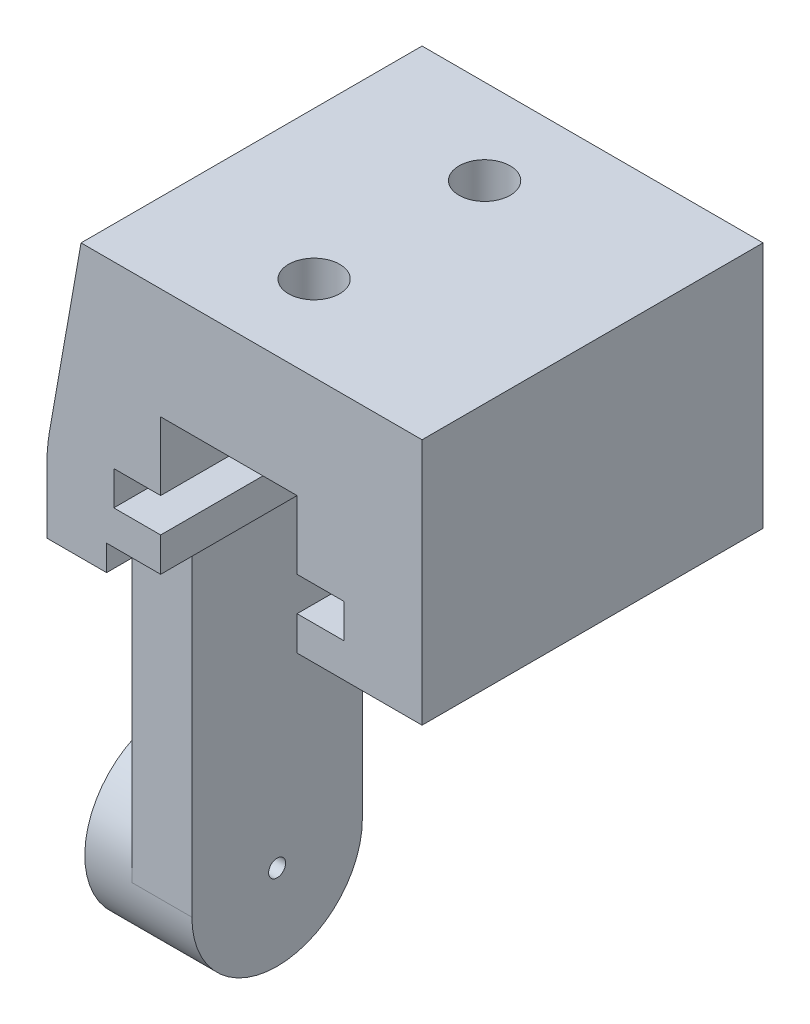
SolidWorks part; units mm, degrees
ref_plane "Front Plane" through (0, 0, 0) normal (0, 0, 1) x (1, 0, 0)
ref_plane "Top Plane" through (0, 0, 0) normal (0, 1, 0) x (1, 0, 0)
ref_plane "Right Plane" through (0, 0, 0) normal (1, 0, 0) x (0, 0, -1)
sketch "Sketch1" plane through (0, 0, 0) normal (0, 0, 1) x (1, 0, 0)
  line L1 (0, 0) -> (22, 0)
  line L2 (0, 0) -> (0, -16)
  line L3 (0, -16) -> (22, -16)
  line L4 (22, 0) -> (22, -16)
  dimension "D1" = 22
  dimension "D2" = 16
extrude "Boss-Extrude1" add sketch "Sketch1" along normal blind 20
chamfer "Chamfer1" distance 2 angle 80 1 edges at (0, 0, 10)
sketch "Sketch2" plane through (0, 0, 20) normal (0, 0, 1) x (1, 0, 0)
  line L0 (3.5, -16) -> (3.5, -14.5)
  line L1 (0, -16) -> (22, -16) construction
  line L2 (3.5, -14.5) -> (6.67, -14.5)
  line L3 (6.67, -14.5) -> (6.67, -12.5)
  line L4 (6.67, -12.5) -> (3.92, -12.5)
  line L5 (3.92, -12.5) -> (3.92, -10.5)
  line L6 (3.92, -10.5) -> (6.67, -10.5)
  line L7 (6.67, -10.5) -> (6.67, -6.5)
  line L8 (6.67, -6.5) -> (14.67, -6.5)
  line L9 (14.67, -6.5) -> (14.67, -10.5)
  line L10 (14.67, -10.5) -> (17.42, -10.5)
  line L11 (17.42, -10.5) -> (17.42, -12.5)
  line L12 (17.42, -12.5) -> (14.67, -12.5)
  line L13 (14.67, -12.5) -> (14.67, -14.5)
  line L14 (14.67, -14.5) -> (22, -14.5)
  line L15 (22, -16) -> (22, 0) construction
  line L16 (22, -14.5) -> (22, -16)
  line L17 (22, -16) -> (3.5, -16)
  dimension "D1" = 3.5
  dimension "D2" = 1.5
  dimension "D3" = 2
  dimension "D4" = 2.75
  dimension "D5" = 2
  dimension "D6" = 4
  dimension "D7" = 8
  dimension "D8" = 3.17
extrude "Cut-Extrude1" cut sketch "Sketch2" against normal up to surface (20 mm away) contours L8 L9 L10 L11 L12 L13 L14 L16 L17 L0 L2 L3 L4 L5 L6 L7 up to face at (9.2, -8.6685, 0)
fillet "Fillet1" radius 10 1 edges at (0, -11.3426, 10)
sketch "Sketch3" plane through (0, -16, 0) normal (0, -1, 0) x (1, 0, 0)
  line L0 (0, 20) -> (0, 0) construction
  line L1 (0, 15) -> (3.5, 15)
  line L2 (0, 15) -> (0, 5)
  line L3 (0, 5) -> (3.5, 5)
  line L4 (3.5, 15) -> (3.5, 5)
  line L5 (3.5, 0) -> (3.5, 20) construction
  line L6 (0, 20) -> (3.5, 20) construction
  dimension "D1" = 5
  dimension "D2" = 10
extrude "Boss-Extrude2" add sketch "Sketch3" along normal blind 20
fillet "Fillet2" radius 1 2 edges
ref_plane "Plane1" through (0, 0, 0) normal (-1, 0, 0) x (0, 0, 1)
sketch "Sketch7" plane through (0, 0, 0) normal (-1, 0, 0) x (0, 0, 1)
  line L0 (15, -36) -> (5, -36) construction
  line L1 (15, -36) -> (5, -36)
  arc A0 (15, -36) -> (5, -36) centre (10, -36) cw
extrude "Boss-Extrude3" add sketch "Sketch7" against normal up to surface (3.5 mm away) up to face at (3.5, -21.7586, 9.6)
sketch "Sketch8" plane through (0, 0, 0) normal (-1, 0, 0) x (0, 0, 1)
  circle A0 centre (10, -36) radius 0.5
  dimension "D1" = 1
extrude "Cut-Extrude2" cut sketch "Sketch8" against normal up to surface (3.5 mm away) up to face at (3.5, -22.2586, 9.6)
sketch "Sketch9" plane through (0, -6.5, 0) normal (0, -1, 0) x (1, 0, 0)
  line L0 (10.67, 20) -> (10.67, 0) construction
  line L1 (6.67, 20) -> (14.67, 20) construction
  line L2 (14.67, 0) -> (6.67, 0) construction
  circle A0 centre (10.67, 15) radius 1.5
  circle A1 centre (10.67, 5) radius 1.5
  dimension "D1" = 3
  dimension "D2" = 5
  dimension "D3" = 5
extrude "Cut-Extrude3" cut sketch "Sketch9" against normal up to surface (6.5 mm away) up to face at (12, 0, 10)
sketch "Sketch10" plane through (0, 0, 0) normal (-1, 0, 0) x (0, 0, 1)
  circle A0 centre (10, -36) radius 5
  circle A1 centre (10, -36) radius 0.5
extrude "Boss-Extrude4" add sketch "Sketch10" along normal blind 2.78
